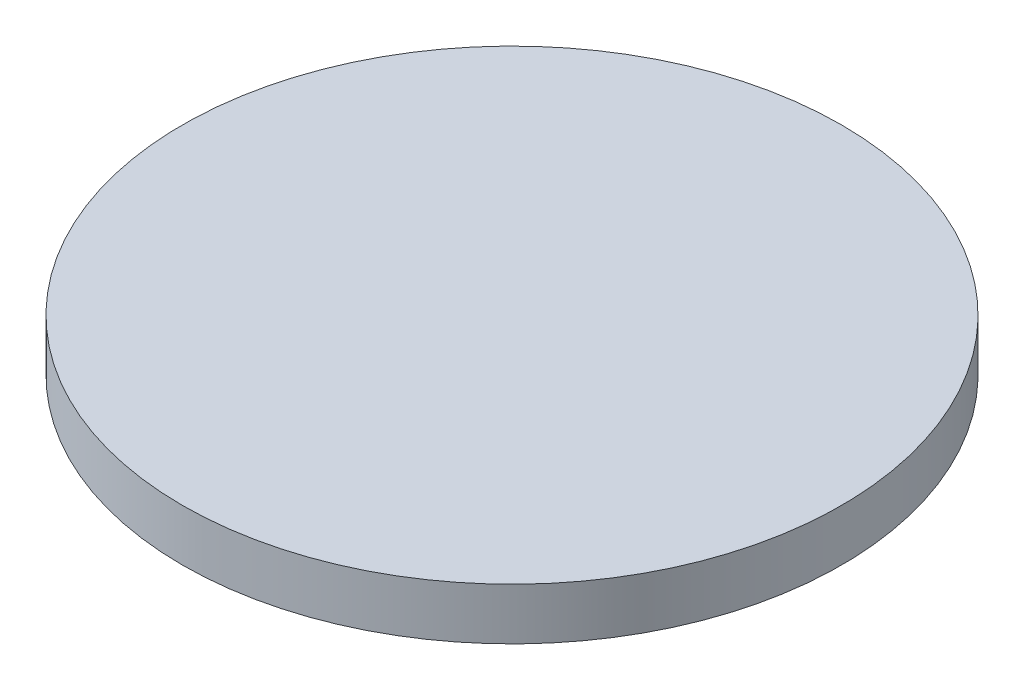
SolidWorks part; units mm, degrees
material "Brass"
ref_plane "Front Plane" through (0, 0, 0) normal (0, 0, 1) x (1, 0, 0)
ref_plane "Top Plane" through (0, 0, 0) normal (0, 1, 0) x (1, 0, 0)
ref_plane "Right Plane" through (0, 0, 0) normal (1, 0, 0) x (0, 0, -1)
sketch "Sketch2" plane through (0, 0, 0) normal (0, 1, 0) x (1, 0, 0)
  circle A0 centre (0, 0) radius 62.5
  circle A1 centre (0, 0) radius 63.75
  circle A2 centre (0, 0) radius 60.9375
  dimension "D1" = 125
  dimension "D2" = 127.5
  dimension "D3" = 2.8125
extrude "Boss-Extrude1" add sketch "Sketch2" along normal mid plane 10 contours A1
sketch "Sketch3" plane through (0, 0, 0) normal (0, 1, 0) x (1, 0, 0)
  line L0 (0, 0) -> (0, 63.75) construction
  line L1 (-0.7143, 62.4959) -> (0.7143, 62.4959) construction
  line L2 (0, 0) -> (-0.4439, 60.9359) construction
  line L3 (-1.5277, 64.732) -> (0, 60.5346) construction
  line L4 (0, 0) -> (2.0024, 63.7185) construction
  arc A0 (-2.2974, 64.7092) -> (-0.4439, 60.9359) centre (-5.2834, 60.9006) cw
  arc A1 (2.2974, 64.7092) -> (0.4439, 60.9359) centre (5.2834, 60.9006) ccw
  circle A2 centre (0, 0) radius 60.9375 construction
  arc A3 (0.4439, 60.9359) -> (-0.4439, 60.9359) centre (0, 0) ccw
  circle A6 centre (0, 0) radius 62.5 construction
  circle A7 centre (0, 0) radius 63.75 construction
  circle A9 centre (0, 0) radius 64.75 construction
  circle A10 centre (0, 0) radius 63.75
  arc A11 (2.2974, 64.7092) -> (-2.2974, 64.7092) centre (0, 0) ccw
  point P10 (0, 0)
  point P15 (64.75, 0)
  point P19 (0.4439, 60.9359)
  point P26 (64.75, 0)
  dimension "D2" = 20
  dimension "D3" = 1.8
  dimension "D1" = 1
equation "\"Module\"= 1.250mm"
equation "\"Number of Teeth\" = 100"
equation "\"D1@Sketch2\"=\"Module\"*\"Number of Teeth\""
equation "\"D3@Sketch2\"=\"Module\"*if( \"Module\"=>1.25,2.25,2.4)"
